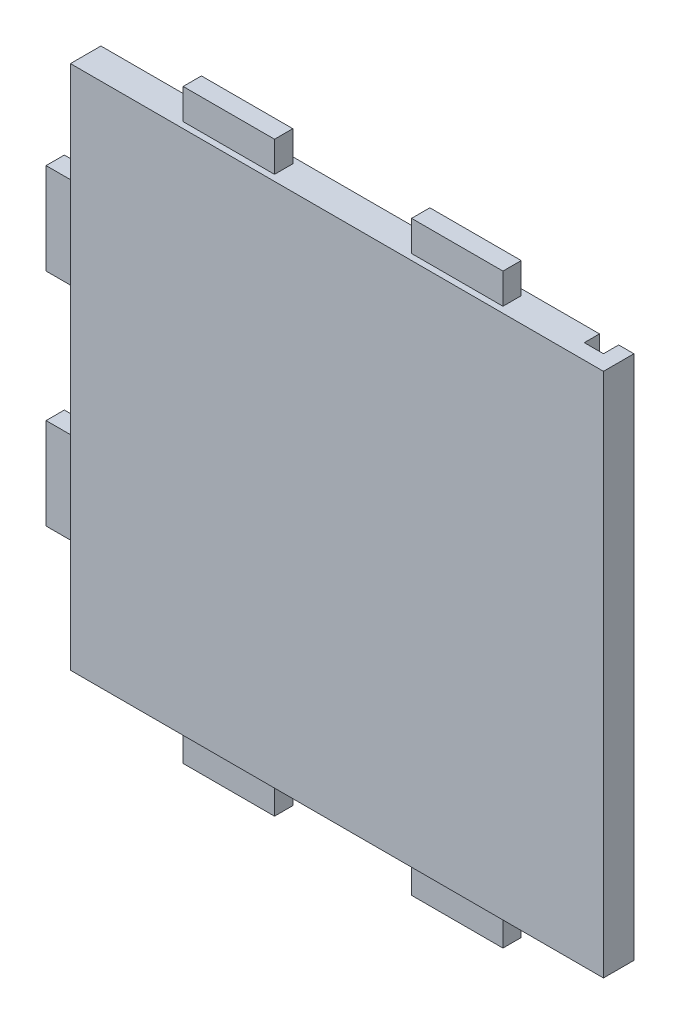
SolidWorks part; units mm, degrees
material "ABS"
ref_plane "Plano frontal" through (0, 0, 0) normal (0, 0, 1) x (1, 0, 0)
ref_plane "Plano superior" through (0, 0, 0) normal (0, 1, 0) x (1, 0, 0)
ref_plane "Plano direito" through (0, 0, 0) normal (1, 0, 0) x (0, 0, -1)
sketch "Esboço1" plane through (0, 0, 0) normal (0, 0, 1) x (1, 0, 0)
  line L1 (87.5, -86.25) -> (-87.5, -86.25)
  line L2 (87.5, -86.25) -> (87.5, 86.25)
  line L3 (87.5, 86.25) -> (-87.5, 86.25)
  line L4 (-87.5, -86.25) -> (-87.5, 86.25)
  line L5 (87.5, -86.25) -> (-87.5, 86.25) construction
  line L6 (87.5, 86.25) -> (-87.5, -86.25) construction
  point P0 (0, 0)
  dimension "D1" = 172.5
  dimension "D2" = 175
extrude "Ressalto-extrusão1" add sketch "Esboço1" along normal blind 10
sketch "Esboço5" plane through (0, 86.25, 0) normal (0, 1, 0) x (1, 0, 0)
  line L0 (0, 0) -> (0, -10) construction
  line L1 (87.5, -10) -> (-87.5, -10) construction
  line L2 (-87.5, -5) -> (87.5, -5) construction
  line L3 (-87.5, -10) -> (-87.5, 0) construction
  line L4 (87.5, -10) -> (87.5, 0) construction
  line L5 (22.5, -2) -> (52.5, -8) construction
  line L6 (-22.5, -8) -> (-52.5, -8)
  line L7 (-22.5, -8) -> (-22.5, -2)
  line L8 (-22.5, -2) -> (-52.5, -2)
  line L9 (-52.5, -8) -> (-52.5, -2)
  line L10 (-22.5, -8) -> (-52.5, -2) construction
  line L11 (-22.5, -2) -> (-52.5, -8) construction
  line L12 (22.5, -8) -> (52.5, -2) construction
  line L13 (52.5, -8) -> (52.5, -2)
  line L14 (22.5, -2) -> (52.5, -2)
  line L15 (22.5, -8) -> (22.5, -2)
  line L16 (22.5, -8) -> (52.5, -8)
  point P11 (-37.5, -5)
  point P20 (37.5, -5)
  dimension "D1" = 30
  dimension "D2" = 6
  dimension "D3" = 50
extrude "Ressalto-extrusão5" add sketch "Esboço5" along normal blind 10
sketch "Esboço6" plane through (-87.5, 0, 0) normal (-1, 0, 0) x (0, 0, 1)
  line L0 (5, 80.8371) -> (5, -100.2795) construction
  line L1 (0, 86.25) -> (0, -86.25) construction
  line L2 (-31.1105, 0) -> (49.0505, 0) construction
  line L3 (10, 86.25) -> (0, 86.25) construction
  line L4 (8, 21.25) -> (2, 21.25)
  line L5 (8, 21.25) -> (8, 51.25)
  line L6 (8, 51.25) -> (2, 51.25)
  line L7 (2, 21.25) -> (2, 51.25)
  line L8 (8, 21.25) -> (2, 51.25) construction
  line L9 (8, 51.25) -> (2, 21.25) construction
  line L10 (8, -51.25) -> (2, -21.25) construction
  line L11 (8, -21.25) -> (2, -51.25) construction
  line L12 (2, -21.25) -> (2, -51.25)
  line L13 (8, -51.25) -> (2, -51.25)
  line L14 (8, -21.25) -> (8, -51.25)
  line L15 (8, -21.25) -> (2, -21.25)
  point P6 (5, 36.25)
  point P19 (5, -36.25)
  dimension "D1" = 5
  dimension "D2" = 6
  dimension "D3" = 30
  dimension "D4" = 50
extrude "Ressalto-extrusão6" add sketch "Esboço6" along normal blind 10
sketch "Esboço7" plane through (0, -86.25, 0) normal (0, -1, 0) x (1, 0, 0)
  line L0 (-118.1326, 5) -> (111.1308, 5) construction
  line L1 (-87.5, 10) -> (87.5, 10) construction
  line L2 (0, -18.9857) -> (0, 24.411) construction
  line L3 (-87.5, 10) -> (-87.5, 0) construction
  line L4 (-22.5, 2) -> (-52.5, 2)
  line L5 (-22.5, 2) -> (-22.5, 8)
  line L6 (-22.5, 8) -> (-52.5, 8)
  line L7 (-52.5, 2) -> (-52.5, 8)
  line L8 (-22.5, 2) -> (-52.5, 8) construction
  line L9 (-22.5, 8) -> (-52.5, 2) construction
  line L10 (22.5, 8) -> (52.5, 2) construction
  line L11 (22.5, 2) -> (52.5, 8) construction
  line L12 (52.5, 2) -> (52.5, 8)
  line L13 (22.5, 8) -> (52.5, 8)
  line L14 (22.5, 2) -> (22.5, 8)
  line L15 (22.5, 2) -> (52.5, 2)
  point P6 (-37.5, 5)
  point P19 (37.5, 5)
  dimension "D1" = 5
  dimension "D2" = 30
  dimension "D3" = 6
  dimension "D4" = 50
extrude "Ressalto-extrusão7" add sketch "Esboço7" along normal blind 10
sketch "Esboço8" plane through (0, 0, 0) normal (0, 0, -1) x (-1, 0, 0)
  line L0 (-117.868, 0) -> (123.9992, 0) construction
  line L1 (-87.5, 86.25) -> (87.5, 86.25) construction
  line L2 (-76.2, -86.25) -> (-82.5, -86.25)
  line L3 (-76.2, -86.25) -> (-76.2, 86.25)
  line L4 (-76.2, 86.25) -> (-82.5, 86.25)
  line L5 (-82.5, -86.25) -> (-82.5, 86.25)
  line L6 (-76.2, -86.25) -> (-82.5, 86.25) construction
  line L7 (-76.2, 86.25) -> (-82.5, -86.25) construction
  line L8 (-87.5, -86.25) -> (-87.5, 86.25) construction
  point P2 (-79.35, 0)
  dimension "D1" = 5
  dimension "D2" = 6.3
extrude "Corte-extrusão1" cut sketch "Esboço8" against normal blind 5
sketch "Esboço9" plane through (-87.5, 0, 0) normal (-1, 0, 0) x (0, 0, 1)
  line L0 (5, 94.9914) -> (5, -96.7804) construction
  line L1 (0, 86.25) -> (0, -86.25) construction
  line L2 (10, -86.25) -> (0, -86.25) construction
  line L3 (-27.2326, 0) -> (31.072, 0) construction
  circle A1 centre (5, -71.25) radius 1.5
  dimension "D2" = 3
  dimension "D3" = 15
  dimension "D1" = 5
extrude "Corte-extrusão2" cut sketch "Esboço9" against normal blind 8
sketch "Esboço10" plane through (0, -86.25, 0) normal (0, -1, 0) x (1, 0, 0)
  line L0 (-109.7376, 5) -> (105.812, 5) construction
  line L1 (-87.5, 10) -> (87.5, 10) construction
  line L2 (87.5, 10) -> (87.5, 0) construction
  circle A0 centre (65, 5) radius 1.5
  dimension "D2" = 3
  dimension "D3" = 22.5
  dimension "D1" = 5
extrude "Corte-extrusão3" cut sketch "Esboço10" against normal blind 8
